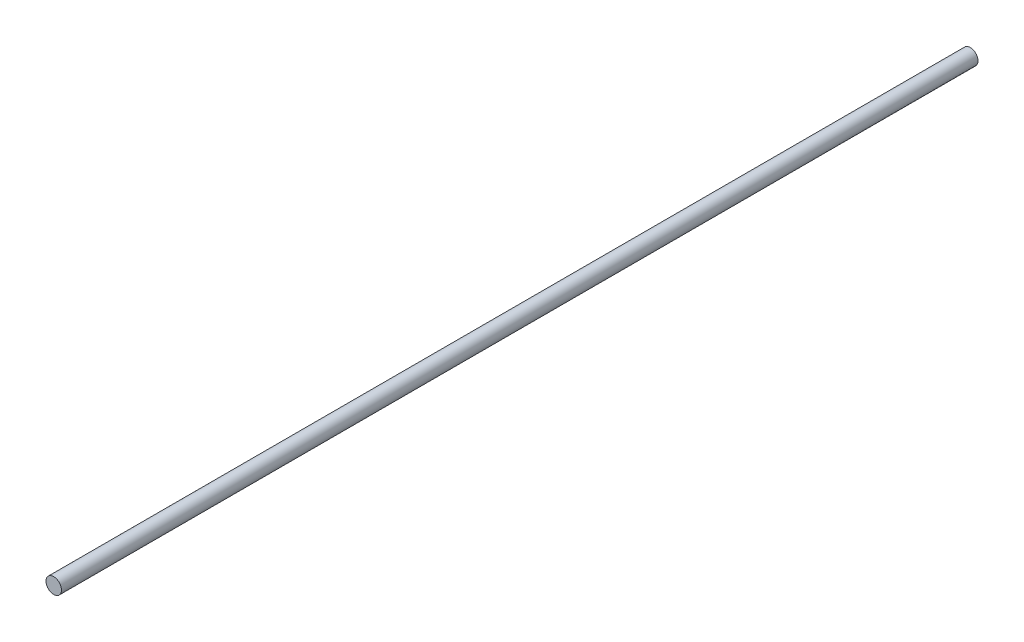
SolidWorks part; units mm, degrees
ref_plane "Front Plane" through (0, 0, 0) normal (0, 0, 1) x (1, 0, 0)
ref_plane "Top Plane" through (0, 0, 0) normal (0, 1, 0) x (1, 0, 0)
ref_plane "Right Plane" through (0, 0, 0) normal (1, 0, 0) x (0, 0, -1)
sketch "Sketch1" plane through (0, 0, 0) normal (0, 0, 1) x (1, 0, 0)
  circle A0 centre (0, 0) radius 4.05
  dimension "D1" = 8.1
extrude "Boss-Extrude1" add sketch "Sketch1" along normal blind 480
